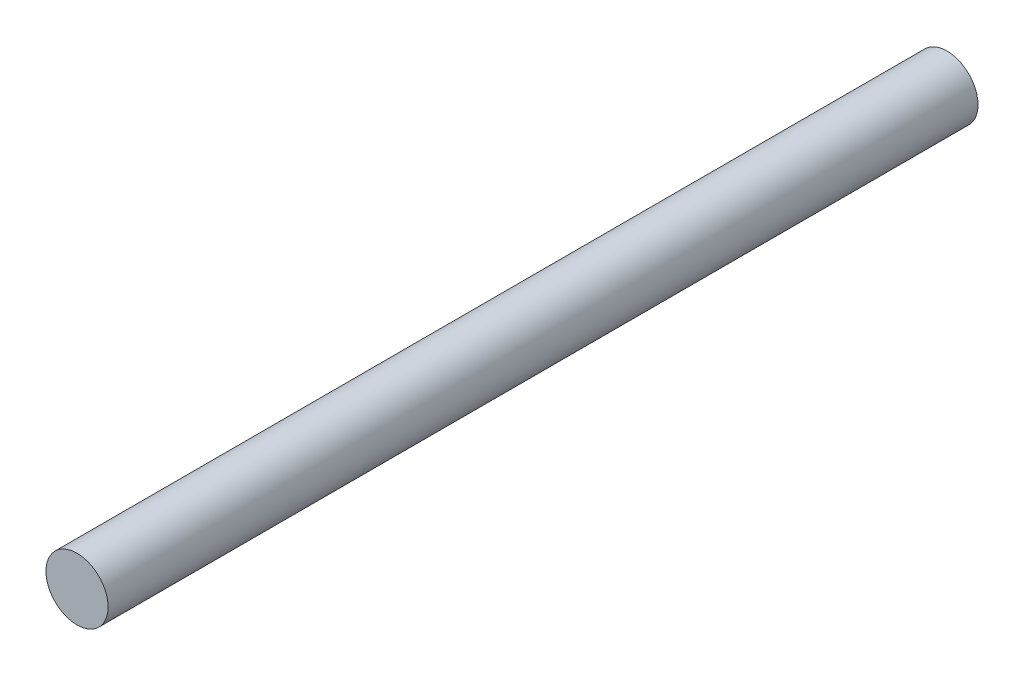
SolidWorks part; units mm, degrees
ref_plane "Front Plane" through (0, 0, 0) normal (0, 0, 1) x (1, 0, 0)
ref_plane "Top Plane" through (0, 0, 0) normal (0, 1, 0) x (1, 0, 0)
ref_plane "Right Plane" through (0, 0, 0) normal (1, 0, 0) x (0, 0, -1)
sketch "Sketch1" plane through (0, 0, 0) normal (0, 0, 1) x (1, 0, 0)
  circle A0 centre (0, 0) radius 1.5875
  dimension "D1" = 3.175
extrude "Boss-Extrude1" add sketch "Sketch1" along normal blind 44.45
